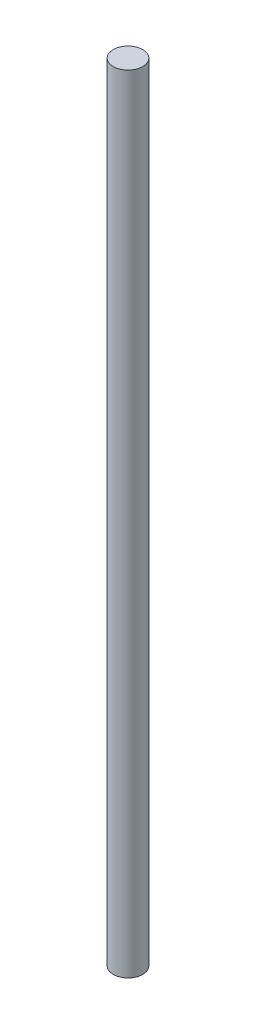
SolidWorks part; units mm, degrees
ref_plane "Front Plane" through (0, 0, 0) normal (0, 0, 1) x (1, 0, 0)
ref_plane "Top Plane" through (0, 0, 0) normal (0, 1, 0) x (1, 0, 0)
ref_plane "Right Plane" through (0, 0, 0) normal (1, 0, 0) x (0, 0, -1)
sketch "Sketch1" plane through (0, 0, 0) normal (0, 1, 0) x (1, 0, 0)
  circle A0 centre (0, 0) radius 1.5
  dimension "D1" = 3
extrude "Boss-Extrude1" add sketch "Sketch1" along normal mid plane 80
